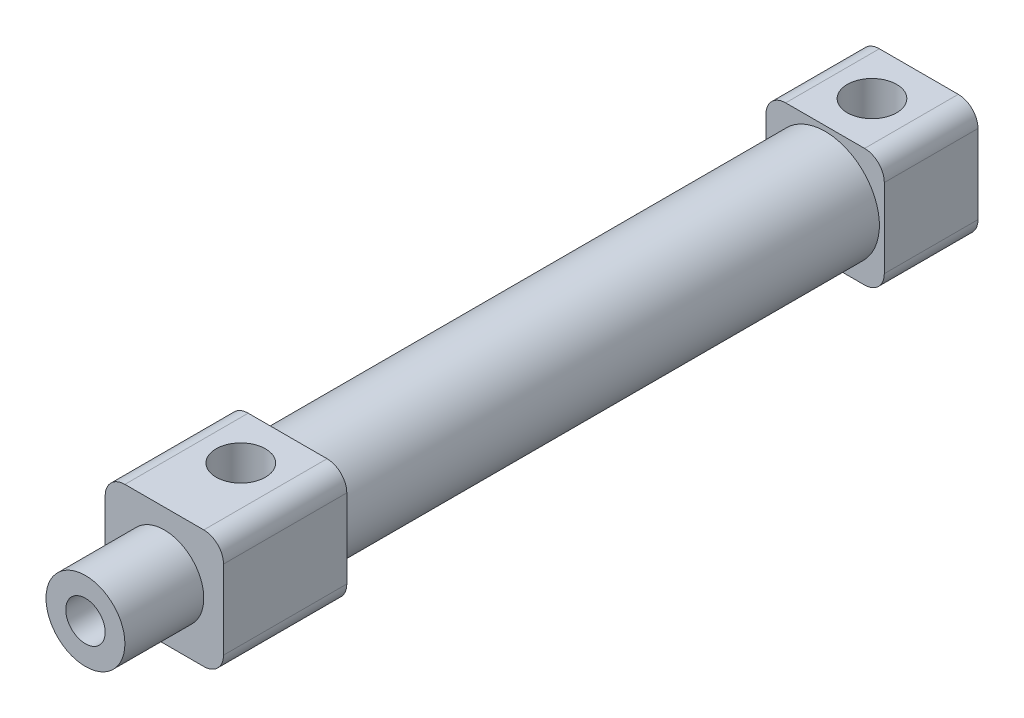
SolidWorks part; units mm, degrees
ref_plane "前视基准面" through (0, 0, 0) normal (0, 0, 1) x (1, 0, 0)
ref_plane "上视基准面" through (0, 0, 0) normal (0, 1, 0) x (1, 0, 0)
ref_plane "右视基准面" through (0, 0, 0) normal (1, 0, 0) x (0, 0, -1)
sketch "草图1" plane through (0, 0, 0) normal (0, 0, 1) x (1, 0, 0)
  line L1 (-6, -6) -> (6, -6)
  line L2 (-6, -6) -> (-6, 6)
  line L3 (-6, 6) -> (6, 6)
  line L4 (6, -6) -> (6, 6)
  line L5 (-6, -6) -> (6, 6) construction
  line L6 (-6, 6) -> (6, -6) construction
  point P0 (0, 0)
  dimension "D1" = 12
  dimension "D2" = 12
extrude "凸台-拉伸1" add sketch "草图1" along normal blind 9.5
sketch "草图2" plane through (0, 0, 9.5) normal (0, 0, 1) x (1, 0, 0)
  circle A0 centre (0, 0) radius 5.5
extrude "凸台-拉伸2" add sketch "草图2" along normal blind 54.5
sketch "草图3" plane through (0, 0, 64) normal (0, 0, 1) x (1, 0, 0)
  line L1 (-6, -6) -> (6, -6)
  line L2 (-6, -6) -> (-6, 6)
  line L3 (-6, 6) -> (6, 6)
  line L4 (6, -6) -> (6, 6)
  line L5 (-6, -6) -> (6, 6) construction
  line L6 (-6, 6) -> (6, -6) construction
  point P0 (0, 0)
extrude "凸台-拉伸3" add sketch "草图3" along normal blind 12.5
sketch "草图4" plane through (0, 0, 76.5) normal (0, 0, 1) x (1, 0, 0)
  circle A0 centre (0, 0) radius 4
extrude "凸台-拉伸4" add sketch "草图4" along normal blind 8
cosmetic thread "装饰螺纹线1" parameters "D2"=6.647
sketch "草图5" plane through (0, 0, 84.5) normal (0, 0, 1) x (1, 0, 0)
  circle A0 centre (0, 0) radius 2
extrude "切除-拉伸1" cut sketch "草图5" against normal offset from surface (83.5 mm away) 1 up to face at (0, 0, 0)
sketch "草图6" plane through (0, 6, 0) normal (0, 1, 0) x (1, 0, 0)
  line L0 (-6, -4.75) -> (6, -4.75) construction
  line L1 (-6, -9.5) -> (-6, 0) construction
  line L2 (6, -9.5) -> (6, 0) construction
  line L3 (-6, -68.75) -> (6, -68.75) construction
  line L5 (-6, -76.5) -> (-6, -64) construction
  line L6 (6, -76.5) -> (6, -64) construction
  line L7 (6, -64) -> (-6, -64) construction
  circle A0 centre (0, -4.75) radius 2.5
  circle A1 centre (0, -68.75) radius 2.5
  dimension "D1" = 5
  dimension "D2" = 4.75
extrude "切除-拉伸2" cut sketch "草图6" against normal up to surface (6 mm away)
cosmetic thread "装饰螺纹线2" parameters "D2"=6
cosmetic thread "装饰螺纹线3" parameters "D2"=6
fillet "圆角1" radius 2 8 edges at (6, 6, 4.75) (6, -6, 4.75) (-6, 6, 4.75) (-6, -6, 4.75) (-6, -6, 70.25) (6, -6, 70.25) (6, 6, 70.25) (-6, 6, 70.25)
